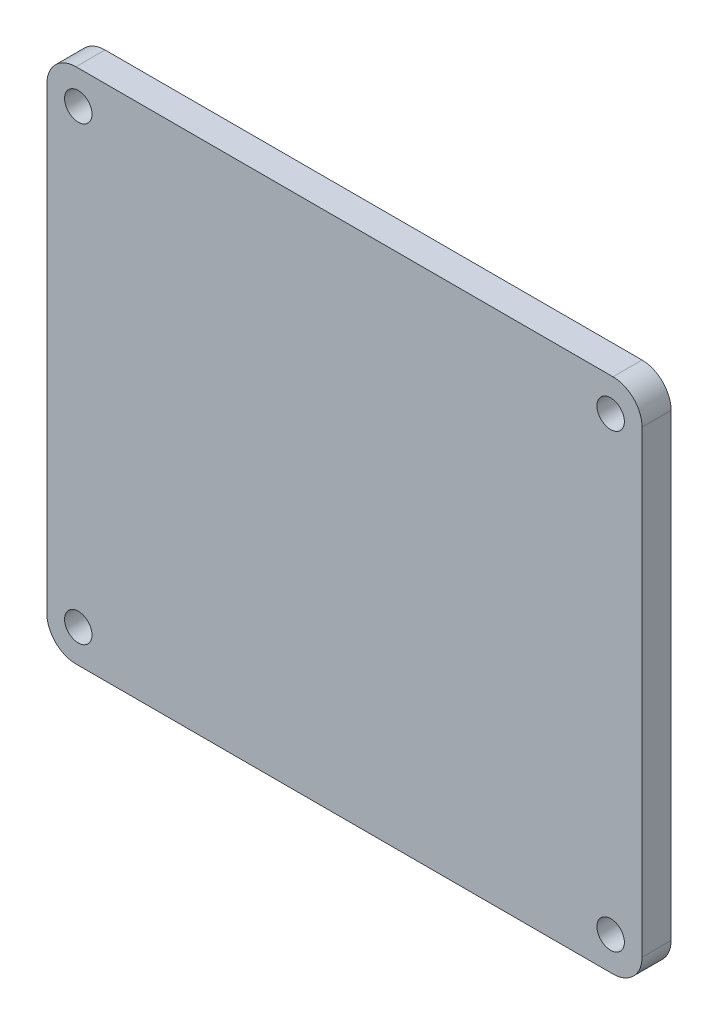
SolidWorks part; units mm, degrees
ref_plane "Front Plane" through (0, 0, 0) normal (0, 0, 1) x (1, 0, 0)
ref_plane "Top Plane" through (0, 0, 0) normal (0, 1, 0) x (1, 0, 0)
ref_plane "Right Plane" through (0, 0, 0) normal (1, 0, 0) x (0, 0, -1)
sketch "Sketch1" plane through (0, 0, 0) normal (0, 1, 0) x (1, 0, 0)
  circle A0 centre (0, 0) radius 25.4
  dimension "D1" = 50.8
ref_plane "Plane1" through (0, 0, 50.8) normal (0, 0, 1) x (1, 0, 0)
sketch "Sketch2" plane through (0, 0, 50.8) normal (0, 0, 1) x (1, 0, 0)
  line L0 (32.512, 20.32) -> (-32.512, 20.32)
  line L1 (-32.512, 20.32) -> (-32.512, 76.835)
  line L2 (-32.512, 76.835) -> (32.512, 76.835)
  line L3 (25.4, 0) -> (-25.4, 0) construction
  line L4 (0, 76.835) -> (0, 20.32) construction
  line L5 (32.512, 20.32) -> (32.512, 76.835)
  dimension "D1" = 20.32
  dimension "D2" = 56.515
  dimension "D3" = 32.512
extrude "Boss-Extrude1" add sketch "Sketch2" against normal blind 3.175
hole_wizard "Ø3.0mm Dowel Hole1" positions "Sketch3" profile "Sketch4" hole size "Ø3.0" standard "ANSI Metric" end condition up to next
sketch "Sketch3" plane through (0, 0, 50.8) normal (0, 0, 1) x (1, 0, 0)
  line L4 (0, -55) -> (0, 55) construction
  line L5 (-32.512, 76.835) -> (-32.512, 20.32) construction
  point P0 (29.083, 73.2155)
  point P2 (29.083, 23.9395)
  point P4 (-29.083, 23.9395)
  point P6 (-29.083, 73.2155)
  point P26 (-32.512, 48.5775)
  dimension "D1" = 58.166
  dimension "D2" = 49.276
  dimension "D3" = 29.083
  dimension "D4" = 24.638
sketch "Sketch4" plane through (29.083, 73.2155, 50.8) normal (1, 0, 0) x (0, -1, 0)
  line L0 (0, 0) -> (0, 3.175)
  line L1 (0, 3.175) -> (1.5, 3.175)
  line L2 (1.5, 3.175) -> (1.5, 0)
  line L5 (1.5, 0) -> (0, 0)
  line L11 (0, -6.35) -> (0, 107.95) construction
  dimension "Thru Hole Dia." = 3
  dimension "Thru Hole Depth" = 3.175
fillet "Fillet1" radius 3.175 4 edges at (-32.512, 76.835, 49.2125) (-32.512, 20.32, 49.2125) (32.512, 20.32, 49.2125) (32.512, 76.835, 49.2125)
ref_plane "Plane2" through (0, 48.5775, 0) normal (0, -1, 0) x (-1, 0, 0)
